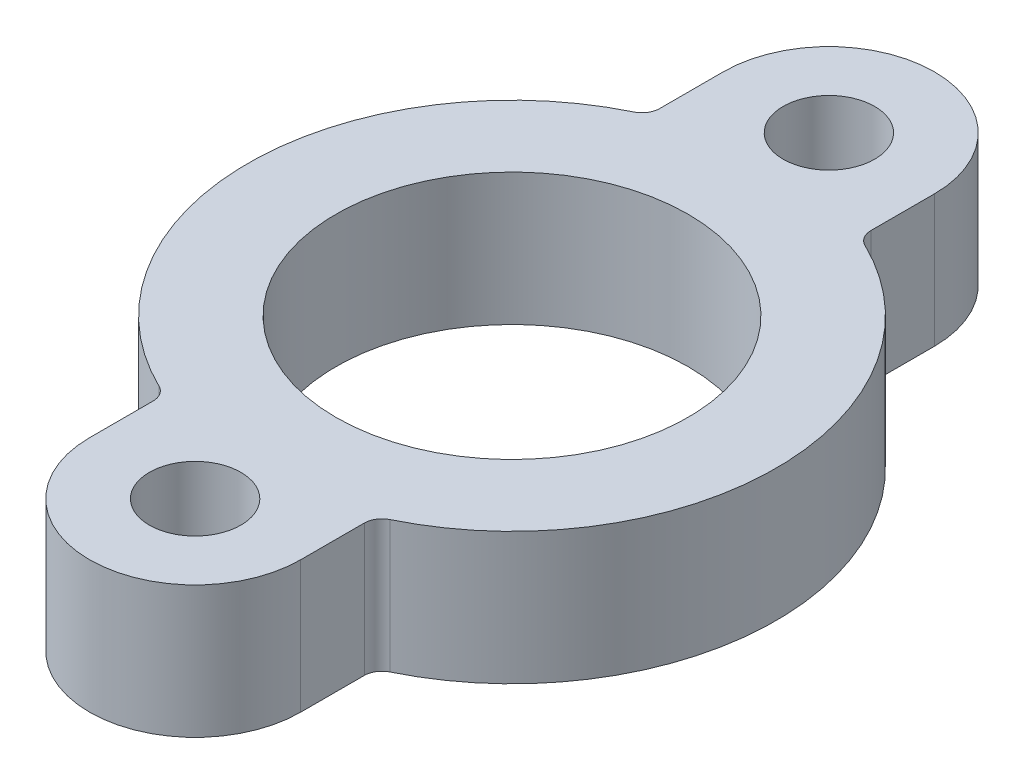
SolidWorks part; units mm, degrees
material "Cast Carbon Steel"
ref_plane "Front Plane" through (0, 0, 0) normal (0, 0, 1) x (1, 0, 0)
ref_plane "Top Plane" through (0, 0, 0) normal (0, 1, 0) x (1, 0, 0)
ref_plane "Right Plane" through (0, 0, 0) normal (1, 0, 0) x (0, 0, -1)
sketch "Sketch1" plane through (0, 0, 0) normal (0, 1, 0) x (1, 0, 0)
  line L0 (7.62, 22.86) -> (7.62, 18.2721)
  line L1 (-7.62, 22.86) -> (-7.62, 18.2721)
  line L2 (7.62, -22.86) -> (7.62, -18.2721)
  line L3 (-7.62, -22.86) -> (-7.62, -18.2721)
  circle A0 centre (0, 0) radius 12.7
  arc A1 (8.3344, -17.1301) -> (8.3344, 17.1301) centre (0, 0) ccw
  arc A2 (7.62, 22.86) -> (-7.62, 22.86) centre (0, 22.86) ccw
  arc A3 (-7.62, -22.86) -> (7.62, -22.86) centre (0, -22.86) ccw
  arc A4 (-8.3344, 17.1301) -> (-8.3344, -17.1301) centre (0, 0) ccw
  circle A5 centre (0, 22.86) radius 3.302
  circle A6 centre (0, -22.86) radius 3.302
  arc A7 (7.62, -18.2721) -> (8.3344, -17.1301) centre (8.89, -18.2721) cw
  arc A8 (-7.62, -18.2721) -> (-8.3344, -17.1301) centre (-8.89, -18.2721) ccw
  arc A9 (-7.62, 18.2721) -> (-8.3344, 17.1301) centre (-8.89, 18.2721) cw
  arc A10 (7.62, 18.2721) -> (8.3344, 17.1301) centre (8.89, 18.2721) ccw
  point P7 (0, 0)
  point P16 (0, 0)
  point P17 (0, 0)
  point P24 (-7.62, 17.4596)
  point P27 (7.62, 17.4596)
  dimension "D3" = 25.4
  dimension "D4" = 38.1
  dimension "D5" = 6.604
  dimension "D6" = 7.62
  dimension "D7" = 1.27
  dimension "D1" = 22.86
  dimension "D2" = 22.86
extrude "Boss-Extrude1" add sketch "Sketch1" along normal blind 9.525
equation "\"D2@Sketch1\"=\"D1@Sketch1\""
